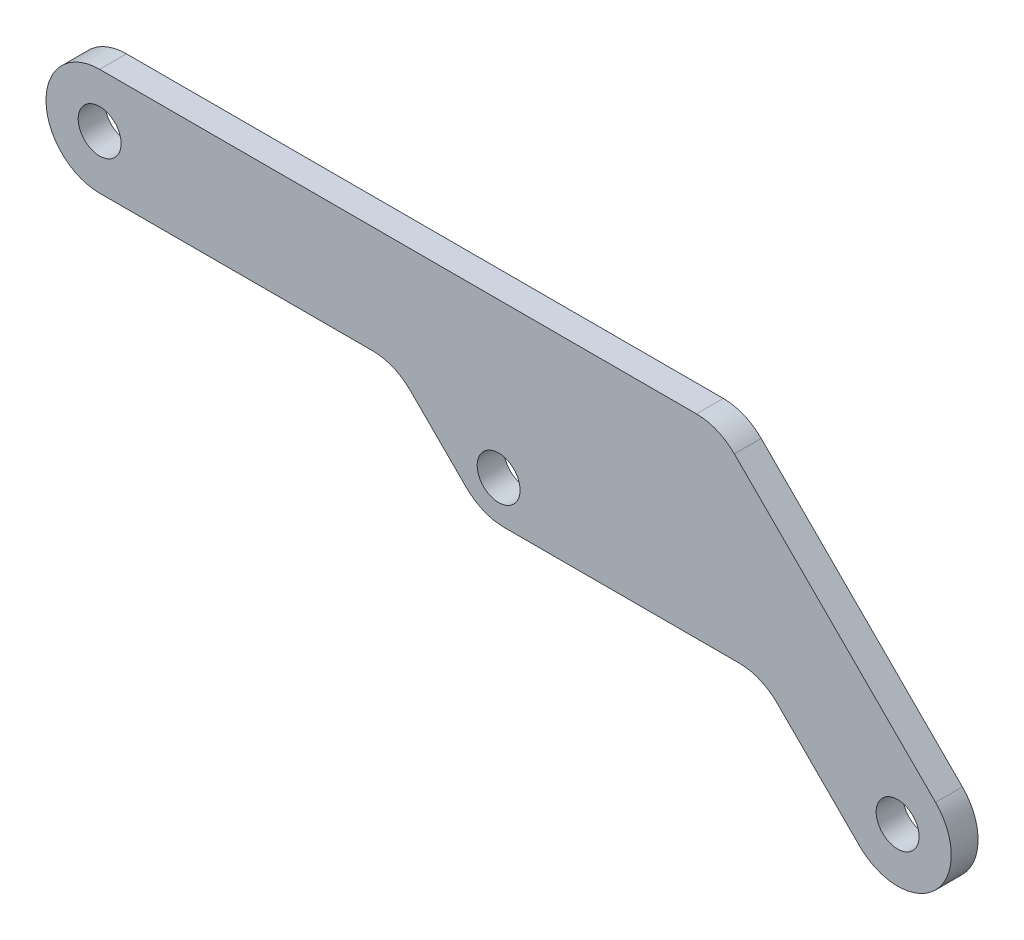
SolidWorks part; units mm, degrees
material "Thornel Mat VMA"
ref_plane "Front Plane" through (0, 0, 0) normal (0, 0, 1) x (1, 0, 0)
ref_plane "Top Plane" through (0, 0, 0) normal (0, 1, 0) x (1, 0, 0)
ref_plane "Right Plane" through (0, 0, 0) normal (1, 0, 0) x (0, 0, -1)
sketch "Sketch1" plane through (0, 0, 0) normal (0, 0, 1) x (1, 0, 0)
  line L0 (-32.9926, -24.6) -> (-26.4926, -31.1)
  line L1 (4.5, -35.6) -> (-55, -20.6) construction
  line L2 (-55, -20.6) -> (-4.8431, -20.6) construction
  line L3 (-55, -16.6) -> (-8.8431, -16.6)
  line L4 (-55, -24.6) -> (-32.9926, -24.6)
  line L5 (-26.4926, -31.1) -> (-5.6569, -31.1)
  line L6 (-25.25, -28.1) -> (-27.3713, -30.2213) construction
  line L7 (-25.25, -28.1) -> (-25.25, -31.1) construction
  line L8 (-5.6569, -31.1) -> (1.6716, -38.4284)
  line L9 (7.3284, -32.7716) -> (-8.8431, -16.6)
  arc A0 (-55, -19) -> (-55, -22.2) centre (-55, -20.6) ccw construction
  circle A1 centre (-25.25, -28.1) radius 1.6
  circle A2 centre (4.5, -35.6) radius 1.6
  circle A3 centre (4.5, -35.6) radius 1.6 construction
  circle A4 centre (-55, -20.6) radius 1.6
  arc A5 (-55, -16.6) -> (-55, -24.6) centre (-55, -20.6) ccw
  arc A6 (1.6716, -38.4284) -> (7.3284, -32.7716) centre (4.5, -35.6) ccw
  point P12 (-29.9216, -20.6)
  dimension "D1" = 3.2
  dimension "D2" = 4
  dimension "D3" = 135
  dimension "D4" = 3
extrude "Boss-Extrude1" add sketch "Sketch1" along normal blind 2
fillet "Fillet1" radius 4 4 edges at (-8.8431, -16.6, 1) (-5.6569, -31.1, 1) (-26.4926, -31.1, 1) (-32.9926, -24.6, 1)
